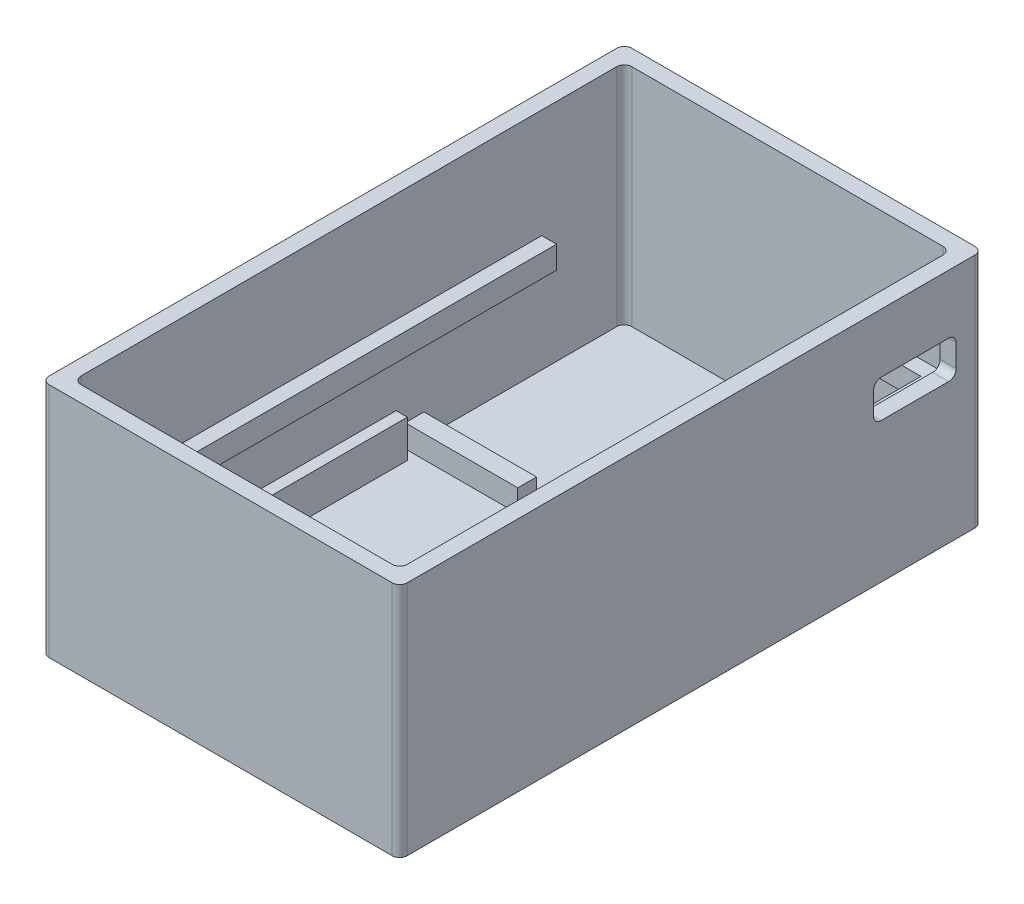
SolidWorks part; units mm, degrees
ref_plane "Front Plane" through (0, 0, 0) normal (0, 0, 1) x (1, 0, 0)
ref_plane "Top Plane" through (0, 0, 0) normal (0, 1, 0) x (1, 0, 0)
ref_plane "Right Plane" through (0, 0, 0) normal (1, 0, 0) x (0, 0, -1)
sketch "PCB Dimensions" plane through (0, 0, 0) normal (0, 1, 0) x (1, 0, 0)
  line L0 (0, 0) -> (-3.5355, 3.5355)
  line L1 (0, 0) -> (40.6457, 0)
  line L2 (0, 0) -> (0, -70.5657)
  line L3 (0, -70.5657) -> (40.6457, -70.5657)
  line L4 (40.6457, 0) -> (40.6457, -70.5657)
  line L5 (40.6457, -70.5657) -> (44.1812, -74.1012)
  line L6 (40.6457, 0) -> (44.1812, 3.5355)
  line L11 (0, -70.5657) -> (-3.5355, -74.1012)
  line L12 (44.1812, -74.1012) -> (-3.5355, -74.1012)
  line L13 (44.1812, -74.1012) -> (44.1812, 3.5355)
  line L14 (44.1812, 3.5355) -> (-3.5355, 3.5355)
  line L15 (-3.5355, -74.1012) -> (-3.5355, 3.5355)
extrude "Boss-Extrude3" add sketch "PCB Dimensions" along normal blind 1.5 contours L14 L15 L12 L13
sketch "Sketch5" plane through (0, 1.5, 0) normal (0, 1, 0) x (1, 0, 0)
  line L0 (-3.5355, 3.5355) -> (-1.4142, 1.4142)
  line L1 (-3.5355, 3.5355) -> (44.1812, 3.5355)
  line L2 (-3.5355, 3.5355) -> (-3.5355, -74.1012)
  line L7 (-3.5355, -74.1012) -> (44.1812, -74.1012)
  line L8 (44.1812, 3.5355) -> (44.1812, -74.1012)
  line L9 (44.1812, -74.1012) -> (42.0599, -71.9799)
  line L11 (-1.4142, 1.4142) -> (42.0599, 1.4142)
  line L12 (-1.4142, 1.4142) -> (-1.4142, -71.9799)
  line L13 (-1.4142, -71.9799) -> (42.0599, -71.9799)
  line L14 (42.0599, 1.4142) -> (42.0599, -71.9799)
extrude "Boss-Extrude5" add sketch "Sketch5" along normal blind 30
fillet "Fillet1" radius 1 8 edges at (42.0599, 16.5, 71.9799) (-3.5355, 15.75, 74.1012) (44.1812, 15.75, 74.1012) (44.1812, 15.75, -3.5355) (-3.5355, 15.75, -3.5355) (-1.4142, 16.5, 71.9799) (42.0599, 16.5, -1.4142) (-1.4142, 16.5, -1.4142)
sketch "Sketch9" plane through (0, 1.5, 0) normal (0, 1, 0) x (1, 0, 0)
  line L3 (0.0799, -70.9799) -> (-1.8581, -70.9799)
  line L9 (0.0799, -28.9799) -> (-1.8581, -28.9799)
  line L10 (-1.8581, -70.9799) -> (-1.8581, -28.9799)
  line L15 (42.5038, -70.9799) -> (42.5038, -28.9799)
  line L16 (40.5658, -28.9799) -> (42.5038, -28.9799)
  line L18 (40.5658, -70.9799) -> (42.5038, -70.9799)
  line L21 (0.0799, -28.9799) -> (0.0799, -70.9799)
  line L23 (40.5658, -28.9799) -> (40.5658, -70.9799)
sketch "Sketch7" plane through (0, 1.5, 0) normal (0, 1, 0) x (1, 0, 0)
  line L3 (-0.4992, 0.4992) -> (41.1449, 0.4992)
  line L4 (-0.4992, 0.4992) -> (-0.4992, -71.0649)
  line L5 (-0.4992, -71.0649) -> (41.1449, -71.0649)
  line L6 (41.1449, 0.4992) -> (41.1449, -71.0649)
extrude "Boss-Extrude6" add sketch "Sketch9" along normal blind 5 contours L21 L3 L10 L9 | L23 L18 L15 L16
sketch "Sketch14" plane through (0, 1.5, 0) normal (0, 1, 0) x (1, 0, 0)
  line L2 (-1.4142, -27.7799) -> (13.5858, -27.7799)
  line L3 (-1.4142, -27.7799) -> (-1.4142, -25.2799)
  line L4 (-1.4142, -25.2799) -> (13.5858, -25.2799)
  line L5 (13.5858, -27.7799) -> (13.5858, -25.2799)
  line L6 (27.0599, -27.7799) -> (27.0599, -25.2799)
  line L7 (42.0599, -25.2799) -> (27.0599, -25.2799)
  line L8 (42.0599, -27.7799) -> (42.0599, -25.2799)
  line L9 (42.0599, -27.7799) -> (27.0599, -27.7799)
extrude "Boss-Extrude7" add sketch "Sketch14" along normal blind 3
sketch "Sketch15" plane through (44.1812, 0, 0) normal (1, 0, 0) x (0, 0, -1)
  line L1 (-73.1012, 31.5) -> (-73.1012, 0) construction
  line L3 (2.5355, 0) -> (2.5355, 31.5) construction
  line L4 (-73.1012, 14) -> (2.5355, 14)
  line L5 (-73.1012, 14) -> (-73.1012, 17)
  line L6 (-73.1012, 17) -> (2.5355, 17)
  line L7 (2.5355, 14) -> (2.5355, 17)
  line M8 (-73.1012, 31.5) -> (-73.1012, 0)
  line M10 (2.5355, 0) -> (2.5355, 31.5)
extrude "Boss-Extrude8" add sketch "Sketch15" against normal blind 46 contours L6 L4 M8 M10
sketch "Sketch17" plane through (0, 17, 0) normal (0, 1, 0) x (1, 0, 0)
  line L3 (40.0842, -63.5437) -> (0.5614, -63.5437)
  line L4 (40.0842, -63.5437) -> (40.0842, -0.5614)
  line L5 (40.0842, -0.5614) -> (0.5614, -0.5614)
  line L6 (0.5614, -63.5437) -> (0.5614, -0.5614)
extrude "Cut-Extrude1" cut sketch "Sketch17" against normal blind 3 contours L5 L6 L3 L4
sketch "Sketch18" plane through (0, 17, 0) normal (0, 1, 0) x (1, 0, 0)
  line L0 (-1.4142, -70.9799) -> (-1.4142, 0.4142) construction
  line L1 (-1.4142, -9.5858) -> (28.5858, -9.5858)
  line L4 (28.5858, -9.5858) -> (28.5858, 1.4142)
  line L5 (-0.4142, 1.4142) -> (41.0599, 1.4142) construction
  line L6 (-0.4142, 1.4142) -> (28.5858, 1.4142)
  line L7 (-1.4142, 0.4142) -> (-1.4142, -9.5858)
  arc A0 (-1.4142, 0.4142) -> (-0.4142, 1.4142) centre (-0.4142, 0.4142) cw
extrude "Cut-Extrude2" cut sketch "Sketch18" against normal blind 3
sketch "Sketch19" plane through (44.1812, 0, 0) normal (1, 0, 0) x (0, 0, -1)
  line L0 (2.5355, 0) -> (2.5355, 17)
  line L1 (2.5355, 0) -> (2.5355, 31.5) construction
  line L2 (0.0355, 23.65) -> (0.0355, 18.65)
  line L11 (0.0355, 18.65) -> (-10.9645, 18.65)
  line L13 (0.0355, 23.65) -> (-10.9645, 23.65)
  line L14 (-10.9645, 18.65) -> (-10.9645, 23.65)
extrude "Cut-Extrude3" cut sketch "Sketch19" against normal blind 10 contours L13 L14 L11 L2
fillet "Fillet2" radius 1 4 edges at (43.1205, 18.65, 10.9645) (43.1205, 18.65, -0.0355) (43.1205, 23.65, -0.0355) (43.1205, 23.65, 10.9645)
scale "Scale1" bodies to scale 113 scale about centroid uniform scaling yes scale factor 0.99
